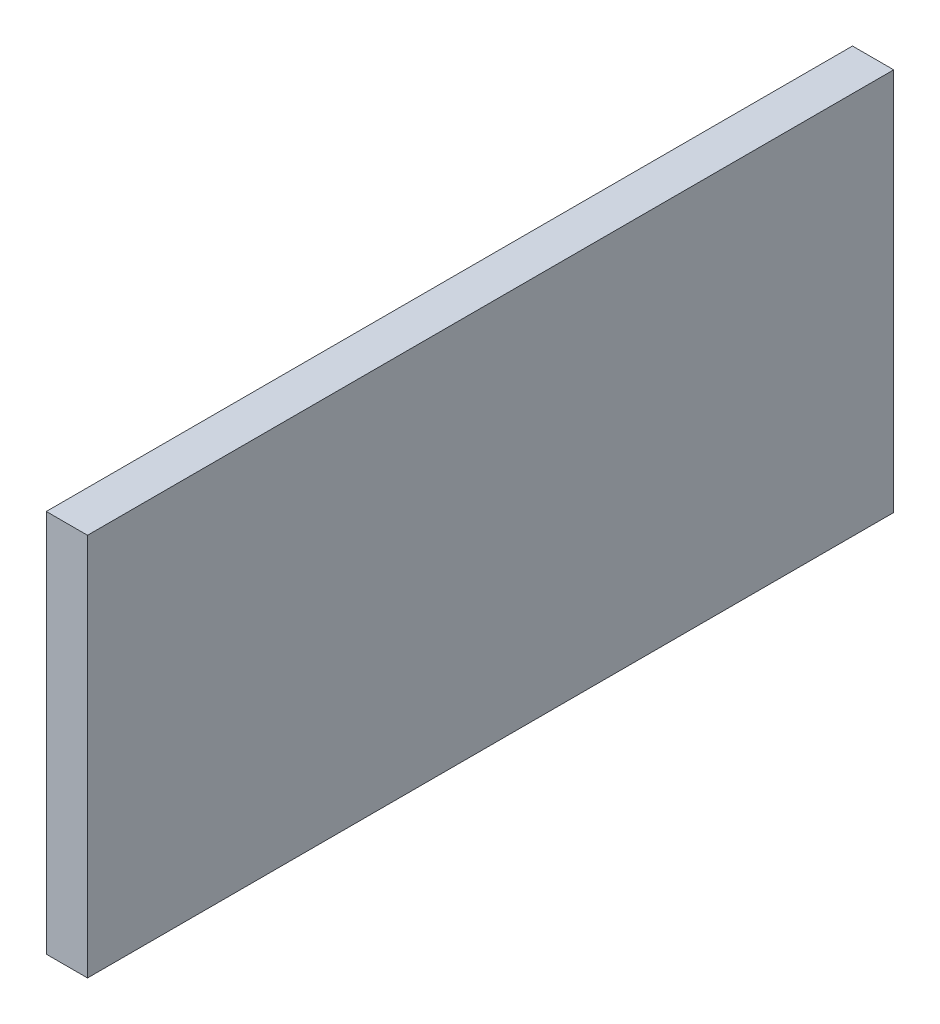
SolidWorks part; units mm, degrees
material "Maple"
ref_plane "Front Plane" through (0, 0, 0) normal (0, 0, 1) x (1, 0, 0)
ref_plane "Top Plane" through (0, 0, 0) normal (0, 1, 0) x (1, 0, 0)
ref_plane "Right Plane" through (0, 0, 0) normal (1, 0, 0) x (0, 0, -1)
sketch "Sketch1" plane through (0, 0, 0) normal (0, 0, 1) x (1, 0, 0)
  line L1 (-1.5875, 14.76) -> (1.5875, 14.76)
  line L2 (-1.5875, 14.76) -> (-1.5875, -14.76)
  line L3 (-1.5875, -14.76) -> (1.5875, -14.76)
  line L4 (1.5875, 14.76) -> (1.5875, -14.76)
  line L5 (-1.5875, 14.76) -> (1.5875, -14.76) construction
  line L6 (-1.5875, -14.76) -> (1.5875, 14.76) construction
  point P0 (0, 0)
  dimension "D1" = 3.175
  dimension "D2" = 29.52
extrude "Boss-Extrude1" add sketch "Sketch1" along normal blind 62.07
equation "\"kerf\"= 0.17 / 2"
equation "\"D2@Sketch1\"=29.35mm + 2*\"kerf\""
equation "\"D1@Boss-Extrude1\"= 61.90mm + 2*\"kerf\""
